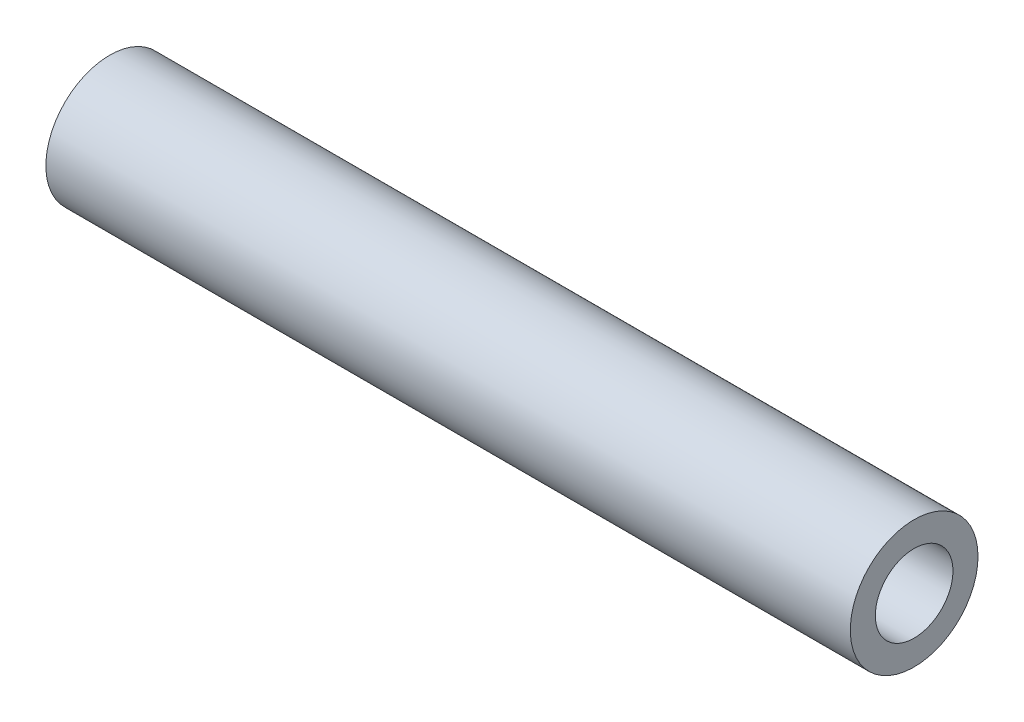
SolidWorks part; units mm, degrees
material "6061-T6 (SS)"
ref_plane "Front" through (0, 0, 0) normal (0, 0, 1) x (1, 0, 0)
ref_plane "Top" through (0, 0, 0) normal (0, 1, 0) x (1, 0, 0)
ref_plane "Right" through (0, 0, 0) normal (1, 0, 0) x (0, 0, -1)
sketch "Sketch1" plane through (0, 0, 0) normal (1, 0, 0) x (0, 0, -1)
  circle A0 centre (0, 0) radius 1.9304
  circle A1 centre (0, 0) radius 3.175
  dimension "D1" = 1.2446
  dimension "D2" = 6.35
extrude "Boss-Extrude1" add sketch "Sketch1" along normal mid plane 40
